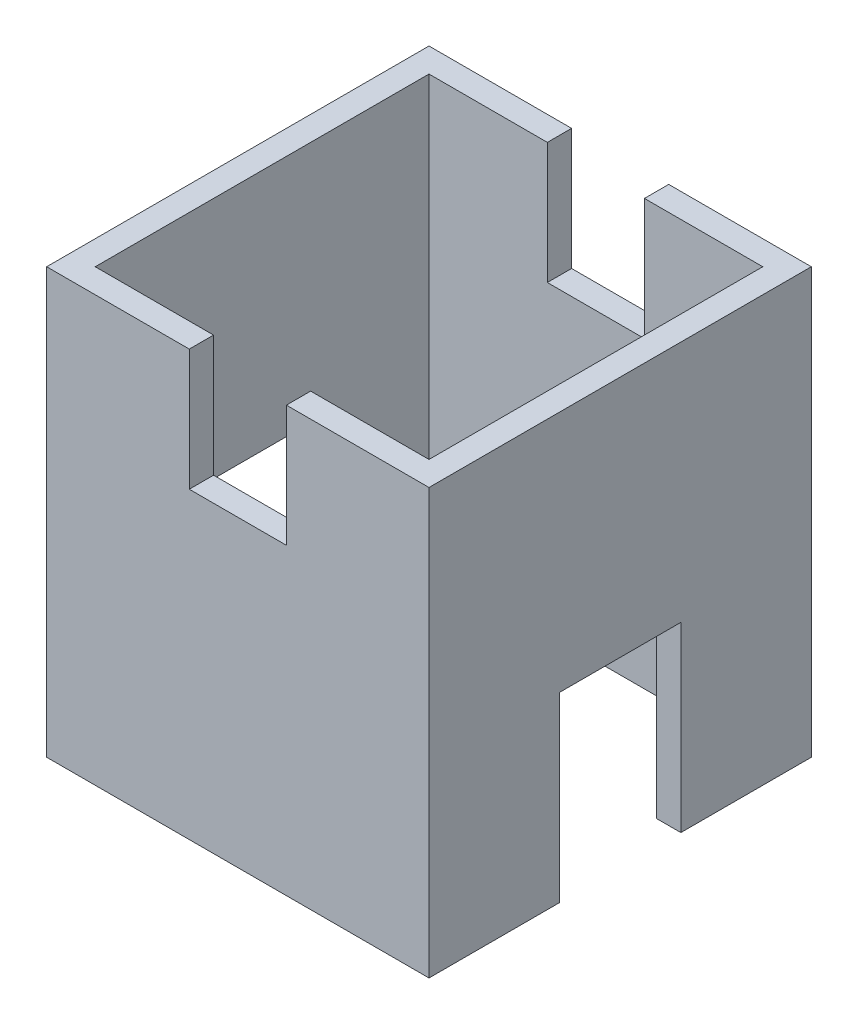
SolidWorks part; units mm, degrees
ref_plane "Front Plane" through (0, 0, 0) normal (0, 0, 1) x (1, 0, 0)
ref_plane "Top Plane" through (0, 0, 0) normal (0, 1, 0) x (1, 0, 0)
ref_plane "Right Plane" through (0, 0, 0) normal (1, 0, 0) x (0, 0, -1)
sketch "Sketch1" plane through (0, 0, 0) normal (0, 1, 0) x (1, 0, 0)
  line L0 (-15.75, -15.75) -> (-15.75, 15.75)
  line L1 (13.75, -13.75) -> (-13.75, -13.75)
  line L2 (13.75, -13.75) -> (13.75, 13.75)
  line L3 (13.75, 13.75) -> (-13.75, 13.75)
  line L4 (-13.75, -13.75) -> (-13.75, 13.75)
  line L5 (13.75, -13.75) -> (-13.75, 13.75) construction
  line L6 (13.75, 13.75) -> (-13.75, -13.75) construction
  line L7 (15.75, 15.75) -> (-15.75, 15.75)
  line L8 (15.75, -15.75) -> (15.75, 15.75)
  line L9 (15.75, -15.75) -> (-15.75, -15.75)
  point P0 (0, 0)
  dimension "D1" = 27.5
  dimension "D2" = 2
extrude "Boss-Extrude1" add sketch "Sketch1" along normal blind 35
sketch "Sketch2" plane through (15.75, 0, 0) normal (1, 0, 0) x (0, 0, -1)
  line L0 (-15.75, 0) -> (15.75, 0) construction
  line L1 (5, 15) -> (-5, 15)
  line L2 (5, 15) -> (5, 0)
  line L3 (5, 0) -> (-5, 0)
  line L4 (-5, 15) -> (-5, 0)
  line L5 (5, 15) -> (-5, 0) construction
  line L6 (5, 0) -> (-5, 15) construction
  line L7 (0, 7.5) -> (0, 0) construction
  point P0 (0, 7.5)
  dimension "D1" = 15
  dimension "D2" = 10
extrude "Cut-Extrude1" cut sketch "Sketch2" against normal through all
sketch "Sketch3" plane through (0, 0, -15.75) normal (0, 0, -1) x (-1, 0, 0)
  line L0 (-15.75, 35) -> (15.75, 35) construction
  line L1 (4, 25) -> (-4, 25)
  line L2 (4, 25) -> (4, 35)
  line L3 (4, 35) -> (-4, 35)
  line L4 (-4, 25) -> (-4, 35)
  line L5 (4, 25) -> (-4, 35) construction
  line L6 (4, 35) -> (-4, 25) construction
  line L7 (0, 0) -> (0, 30) construction
  line L8 (-15.75, 0) -> (15.75, 0) construction
  point P0 (0, 30)
  dimension "D1" = 8
  dimension "D2" = 10
extrude "Cut-Extrude2" cut sketch "Sketch3" against normal through all
